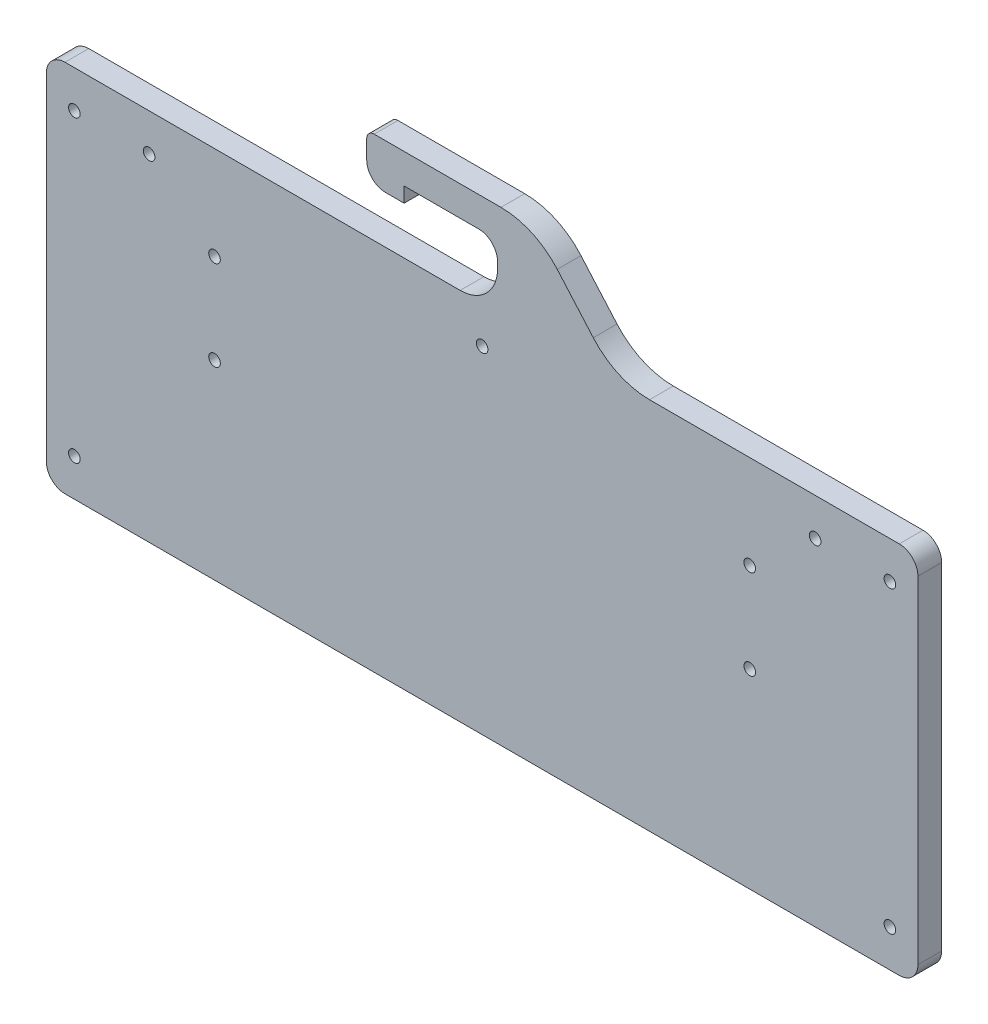
SolidWorks part; units mm, degrees
ref_plane "Front Plane" through (0, 0, 0) normal (0, 0, 1) x (1, 0, 0)
ref_plane "Top Plane" through (0, 0, 0) normal (0, 1, 0) x (1, 0, 0)
ref_plane "Right Plane" through (0, 0, 0) normal (1, 0, 0) x (0, 0, -1)
sketch "Sketch1" plane through (0, 0, 0) normal (0, 0, 1) x (1, 0, 0)
  line L0 (116.6, 0) -> (116.6, -35.2914) construction
  line L1 (0, 0) -> (233.2, 0)
  line L2 (0, 0) -> (0, -100)
  line L3 (0, -100) -> (233.2, -100)
  line L4 (233.2, 0) -> (233.2, -100)
  line L5 (0, 0) -> (15, 0)
  line L6 (0, 0) -> (0, -100)
  line L7 (0, -100) -> (15, -100)
  line L9 (233.2, 0) -> (218.2, 0)
  line L10 (233.2, 0) -> (233.2, -100)
  line L11 (233.2, -100) -> (218.2, -100)
  line L13 (0, -50) -> (37.696, -50) construction
  circle A0 centre (7.5, -10) radius 1.55
  circle A1 centre (225.7, -10) radius 1.55
  circle A2 centre (7.5, -90) radius 1.55
  circle A3 centre (225.7, -90) radius 1.55
  circle A4 centre (27.5, -10) radius 1.55
  circle A5 centre (205.7, -10) radius 1.55
  circle A6 centre (116.6, -10) radius 1.55
  dimension "D5" = 3.1
  dimension "D7" = 3.1
  dimension "D8" = 3.1
  dimension "D11" = 3.1
  dimension "D1" = 100
  dimension "D2" = 233.2
  dimension "D3" = 15
  dimension "D4" = 15
  dimension "D6" = 10
  dimension "D9" = 20
  dimension "D10" = 20
extrude "Boss-Extrude1" add sketch "Sketch1" along normal blind 6.35 contours L4 L1 L2 L3 A3 A1 A0 A2
fillet "Fillet1" radius 5 4 edges at (233.2, -100, 3.175) (0, -100, 3.175) (0, 0, 3.175) (233.2, 0, 3.175)
sketch "Sketch2" plane through (0, 0, 6.35) normal (0, 0, 1) x (1, 0, 0)
  line L0 (116.6, 0) -> (116.6, -100) construction
  line L1 (5, 0) -> (228.2, 0) construction
  line L2 (5, -100) -> (228.2, -100) construction
  line L3 (0, -5) -> (0, -95) construction
  circle A0 centre (45, -25) radius 1.55
  circle A1 centre (45, -49) radius 1.55
  circle A2 centre (188.2, -49) radius 1.55
  circle A3 centre (188.2, -25) radius 1.55
  dimension "D1" = 3.1
  dimension "D3" = 3.1
  dimension "D2" = 45
  dimension "D4" = 24
  dimension "D5" = 25
extrude "Cut-Extrude1" cut sketch "Sketch2" against normal blind 6.35 contours A0 | A1 | A2 | A3
sketch "Sketch3" plane through (0, 0, 6.35) normal (0, 0, 1) x (1, 0, 0)
  line L0 (5, 0) -> (228.2, 0) construction
  line L1 (120.7236, 0) -> (130.7236, 0)
  line L2 (120.7236, 0) -> (120.7236, 12.7)
  line L3 (120.7236, 12.7) -> (130.7236, 12.7)
  line L4 (130.7236, 0) -> (130.7236, 12.7)
  line L5 (130.7236, 24.7) -> (152.3136, 0)
  line L6 (130.7236, 12.7) -> (85.7236, 12.7)
  line L7 (130.7236, 12.7) -> (130.7236, 24.7)
  line L8 (130.7236, 24.7) -> (85.7236, 24.7)
  line L9 (85.7236, 12.7) -> (85.7236, 24.7)
  line L10 (120.7236, 12.7) -> (95.7236, 12.7)
  line L11 (120.7236, 12.7) -> (120.7236, 16.7)
  line L12 (120.7236, 16.7) -> (95.7236, 16.7)
  line L13 (95.7236, 12.7) -> (95.7236, 16.7)
  line M11 (228.2, 0) -> (5, 0)
  dimension "D1" = 12.7
  dimension "D2" = 10
  dimension "D3" = 12
  dimension "D4" = 45
  dimension "D5" = 25
  dimension "D6" = 4
extrude "Boss-Extrude2" add sketch "Sketch3" against normal up to surface (6.35 mm away) contours L4 L3 L2 M11 | L6 L13 L12 L11 L3 L7 L8 L9 | L7 L4 L5 M11 up to face at (46.55, -49, 0)
fillet "Fillet2" radius 5 1 edges at (85.7236, 12.7, 3.175)
fillet "Fillet3" radius 10 1 edges at (120.7236, 0, 3.175)
fillet "Fillet4" radius 2 1 edges at (85.7236, 24.7, 3.175)
fillet "Fillet5" radius 20 2 edges at (130.7236, 24.7, 3.175) (152.3136, 0, 3.175)
fillet "Fillet6" radius 5 1 edges at (120.7236, 16.7, 3.175)
